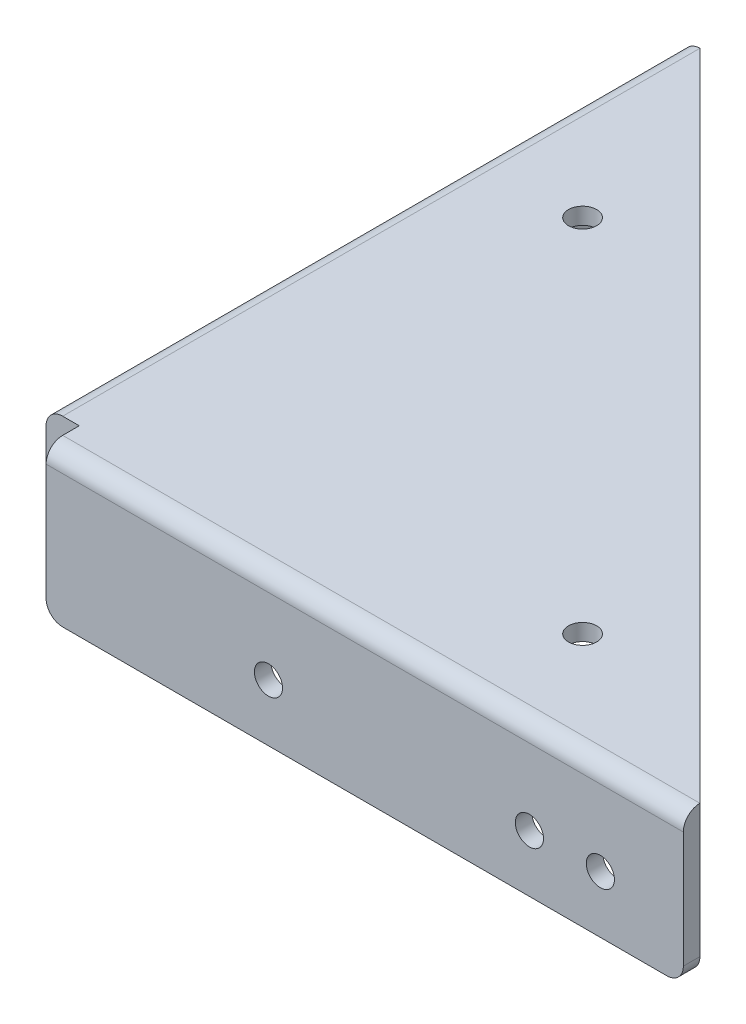
SolidWorks part; units mm, degrees
ref_plane "Front Plane" through (0, 0, 0) normal (0, 0, 1) x (1, 0, 0)
ref_plane "Top Plane" through (0, 0, 0) normal (0, 1, 0) x (1, 0, 0)
ref_plane "Right Plane" through (0, 0, 0) normal (1, 0, 0) x (0, 0, -1)
sketch "Sketch1" plane through (0, 0, 0) normal (0, 1, 0) x (1, 0, 0)
  line L0 (0, 0) -> (0, 102.616)
  line L1 (2.54, 102.616) -> (102.616, 2.54)
  line L2 (102.616, 0) -> (0, 0)
  line L3 (0, 102.616) -> (2.54, 102.616)
  line L4 (2.54, 102.616) -> (2.54, 2.54)
  line L5 (2.54, 2.54) -> (102.616, 2.54)
  line L6 (102.616, 2.54) -> (102.616, 0)
  dimension "D1" = 102.616
  dimension "D2" = 102.616
  dimension "D3" = 2.54
  dimension "D4" = 2.54
extrude "Boss-Extrude3" add sketch "Sketch1" along normal blind 22.86 contours L6 L5 L4 L3 L0 L2
sketch "Sketch3" plane through (0, 22.86, 0) normal (0, 1, 0) x (1, 0, 0)
  line L0 (2.54, 102.616) -> (102.616, 2.54)
  line L1 (102.616, 2.54) -> (2.54, 2.54)
  line L2 (2.54, 2.54) -> (2.54, 102.616)
extrude "Boss-Extrude4" add sketch "Sketch3" against normal blind 2.54
fillet "Fillet1" radius 2.54 5 edges at (0, 22.86, -51.308) (51.308, 22.86, 0) (2.54, 10.16, -2.54) (52.578, 20.32, -2.54) (2.54, 20.32, -52.578)
sketch "Sketch4" plane through (0, 20.32, 0) normal (0, -1, 0) x (1, 0, 0)
  line L0 (5.08, -5.08) -> (5.08, 2.1798)
  line L1 (5.08, 2.1798) -> (-2.9244, 2.1798)
  line L2 (-2.9244, 2.1798) -> (-2.9244, -5.08)
  line L3 (-2.9244, -5.08) -> (5.08, -5.08)
extrude "Cut-Extrude1" cut sketch "Sketch4" against normal blind 2.54 and the other way blind 32.004
hole_wizard "#8 Clearance Hole1" positions "Sketch6" profile "Sketch5" hole size "#8" standard "ANSI Inch"
sketch "Sketch6" plane through (2.54, 0, 0) normal (1, 0, 0) x (0, 0, -1)
  line L0 (102.616, 17.78) -> (102.616, 0) construction
  line L1 (102.616, 0) -> (5.08, 0) construction
  point P0 (39.116, 8.7312)
  point P2 (89.916, 8.7312)
  dimension "D1" = 12.7
  dimension "D2" = 8.7312
  dimension "D3" = 50.8
sketch "Sketch5" plane through (2.54, 8.7312, -39.116) normal (0, 1, 0) x (0, 0, -1)
  line L0 (0, 0) -> (0, 75.7154)
  line L1 (0, 75.7154) -> (2.1526, 74.422)
  line L2 (2.1526, 74.422) -> (2.1526, 0)
  line L5 (2.1526, 0) -> (0, 0)
  line L10 (0, 75.7154) -> (-2.1527, 74.422) construction
  line L11 (0, -6.35) -> (0, 107.95) construction
  dimension "Hole Dia." = 4.3053
  dimension "Hole Depth" = 74.422
  dimension "Drill Angle" = 118
hole_wizard "#8 Clearance Hole2" positions "Sketch8" profile "Sketch7" hole size "#8" standard "ANSI Inch"
sketch "Sketch8" plane through (0, 0, 0) normal (0, 0, 1) x (1, 0, 0)
  line L0 (102.616, 0) -> (5.08, 0) construction
  line L1 (102.616, 20.32) -> (102.616, 0) construction
  point P0 (89.916, 8.7312)
  point P2 (39.116, 8.7312)
  dimension "D1" = 8.7312
  dimension "D2" = 12.7
  dimension "D3" = 50.8
sketch "Sketch7" plane through (89.916, 8.7312, 0) normal (1, 0, 0) x (0, -1, 0)
  line L0 (0, 0) -> (0, 75.7154)
  line L1 (0, 75.7154) -> (2.1526, 74.422)
  line L2 (2.1526, 74.422) -> (2.1526, 0)
  line L5 (2.1526, 0) -> (0, 0)
  line L10 (0, 75.7154) -> (-2.1527, 74.422) construction
  line L11 (0, -6.35) -> (0, 107.95) construction
  dimension "Hole Dia." = 4.3053
  dimension "Hole Depth" = 74.422
  dimension "Drill Angle" = 118
hole_wizard "#8 Clearance Hole3" positions "Sketch10" profile "Sketch9" hole size "#8" standard "ANSI Inch"
sketch "Sketch10" plane through (0, 20.32, 0) normal (0, -1, 0) x (-1, 0, 0)
  line L0 (-16.0104, 71.1851) -> (-29.5788, 84.7536) construction
  line L1 (-71.1851, 16.0104) -> (-89.1423, 33.9676) construction
  line L5 (-100.076, 5.08) -> (-5.08, 100.076) construction
  point P0 (-16.0104, 71.1851)
  point P2 (-71.1851, 16.0104)
  dimension "D1" = 31.75
  dimension "D2" = 31.75
  dimension "D3" = 12.7
  dimension "D4" = 12.7
sketch "Sketch9" plane through (16.0104, 20.32, -71.1851) normal (1, 0, 0) x (0, 0, -1)
  line L0 (0, 0) -> (0, 75.7154)
  line L1 (0, 75.7154) -> (2.1526, 74.422)
  line L2 (2.1526, 74.422) -> (2.1526, 0)
  line L5 (2.1526, 0) -> (0, 0)
  line L10 (0, 75.7154) -> (-2.1527, 74.422) construction
  line L11 (0, -6.35) -> (0, 107.95) construction
  dimension "Hole Dia." = 4.3053
  dimension "Hole Depth" = 74.422
  dimension "Drill Angle" = 118
fillet "Fillet2" radius 2.54 4 edges at (1.27, 0, -102.616) (102.616, 0, -1.27) (1.27, 0, -5.08) (5.08, 0, -1.27)
sketch "Sketch11" plane through (2.54, 0, 0) normal (1, 0, 0) x (0, 0, -1)
  line L0 (79.0575, 8.7312) -> (89.916, 8.7312) construction
  circle A0 centre (79.0575, 8.7312) radius 2.159
  dimension "D2" = 4.318
  dimension "D1" = 10.8585
extrude "Cut-Extrude2" cut sketch "Sketch11" against normal blind 7.62
sketch "Sketch12" plane through (0, 0, 0) normal (0, 0, 1) x (1, 0, 0)
  line L0 (79.0575, 8.7313) -> (89.916, 8.7312) construction
  circle A0 centre (79.0575, 8.7313) radius 2.159
  dimension "D2" = 4.318
  dimension "D1" = 10.8585
extrude "Cut-Extrude3" cut sketch "Sketch12" against normal blind 7.62
